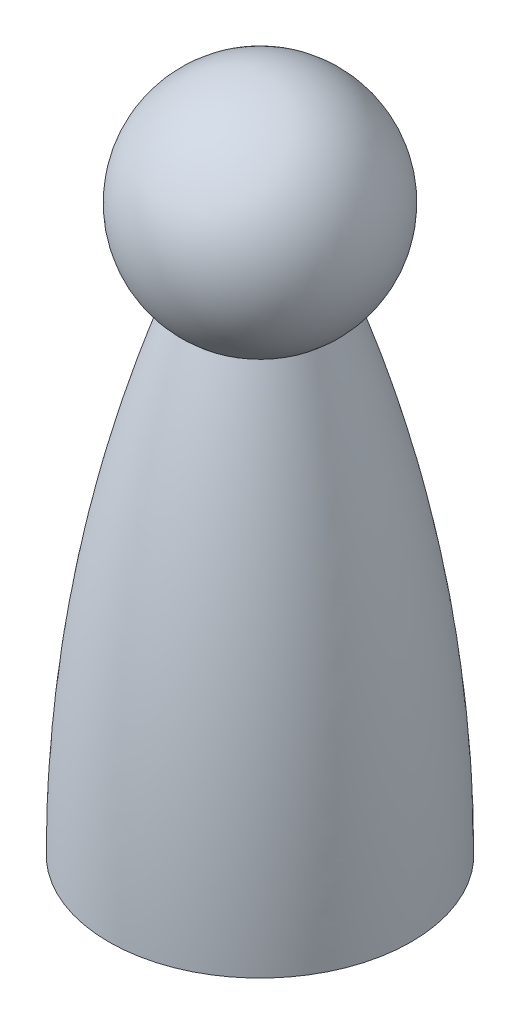
SolidWorks part; units mm, degrees
ref_plane "Front Plane" through (0, 0, 0) normal (0, 0, 1) x (1, 0, 0)
ref_plane "Top Plane" through (0, 0, 0) normal (0, 1, 0) x (1, 0, 0)
ref_plane "Right Plane" through (0, 0, 0) normal (1, 0, 0) x (0, 0, -1)
sketch "Sketch1" plane through (0, 0, 0) normal (1, 0, 0) x (0, 0, -1)
  line L0 (0, 0) -> (0, 88.9)
  line L1 (0, 0) -> (12.7, 0)
  line L2 (12.7, 0) -> (12.7, 3.81)
  line L3 (12.7, 3.81) -> (19.05, 3.81)
  arc A0 (0, 60.96) -> (0, 88.9) centre (0, 74.93) ccw
  spline S0 degree 2 poles (19.05, 3.81) (18.9607, 34.8743) (8.6595, 63.9676) knots 0 0 0 1 1 1
  point P8 (0, 0)
  point P12 (8.6595, 63.9676)
  dimension "D2" = 27.94
  dimension "D1" = 88.9
  dimension "D3" = 12.7
  dimension "D4" = 3.81
  dimension "D5" = 8.6595
  dimension "D6" = 19.6712
  dimension "D7" = 15.0745
  dimension "D8" = 6.35
revolve "Revolve1" add sketch "Sketch1" angle 360 about L0
